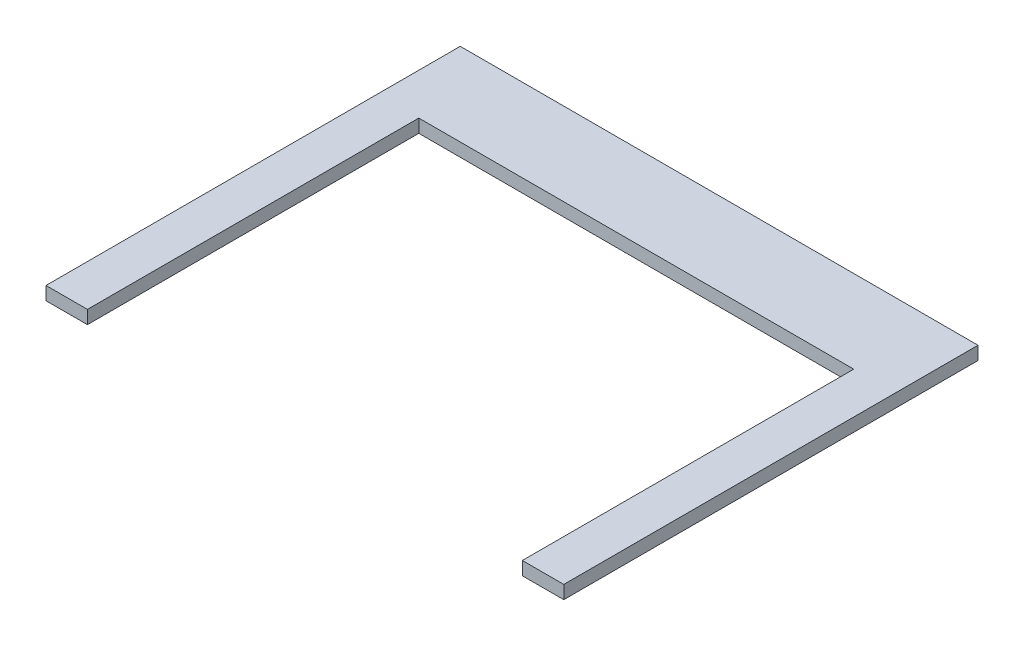
SolidWorks part; units mm, degrees
material "6061-T6 (SS)"
ref_plane "Front Plane" through (0, 0, 0) normal (0, 0, 1) x (1, 0, 0)
ref_plane "Top Plane" through (0, 0, 0) normal (0, 1, 0) x (1, 0, 0)
ref_plane "Right Plane" through (0, 0, 0) normal (1, 0, 0) x (0, 0, -1)
sketch "Sketch1" plane through (0, 0, 0) normal (0, 1, 0) x (1, 0, 0)
  line L0 (-79.375, 0) -> (-66.675, 0)
  line L1 (79.375, 0) -> (79.375, 127)
  line L2 (79.375, 127) -> (-79.375, 127)
  line L3 (-79.375, 127) -> (-79.375, 0)
  line L4 (-66.675, 101.6) -> (66.675, 101.6)
  line L5 (66.675, 101.6) -> (66.675, 0)
  line L6 (66.675, 0) -> (79.375, 0)
  line L7 (-66.675, 0) -> (-66.675, 101.6)
  point P7 (0, 0)
  point P10 (0, 101.6)
  point P11 (0, 0)
  dimension "D1" = 133.35
  dimension "D2" = 158.75
  dimension "D3" = 12.7
  dimension "D4" = 127
  dimension "D5" = 25.4
extrude "Boss-Extrude1" add sketch "Sketch1" along normal blind 4.064
